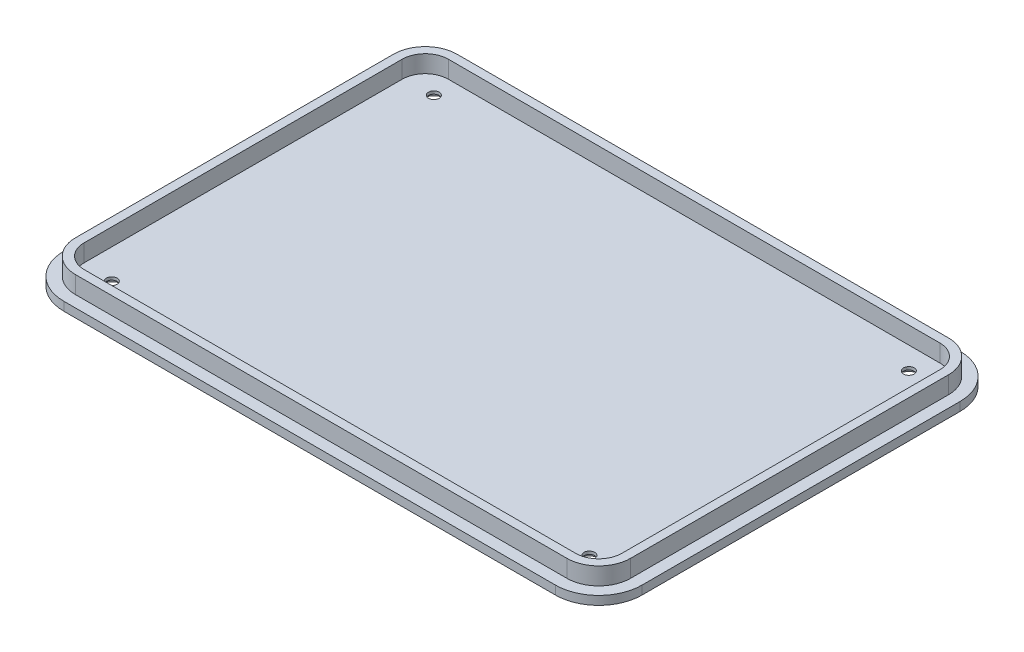
SolidWorks part; units mm, degrees
ref_plane "Front Plane" through (0, 0, 0) normal (0, 0, 1) x (1, 0, 0)
ref_plane "Top Plane" through (0, 0, 0) normal (0, 1, 0) x (1, 0, 0)
ref_plane "Right Plane" through (0, 0, 0) normal (1, 0, 0) x (0, 0, -1)
sketch "Sketch1" plane through (0, 0, 0) normal (0, 1, 0) x (1, 0, 0)
  line L1 (-100, 70) -> (100, 70)
  line L2 (-100, 70) -> (-100, -70)
  line L3 (-100, -70) -> (100, -70)
  line L4 (100, 70) -> (100, -70)
  line L5 (-100, 70) -> (100, -70) construction
  line L6 (-100, -70) -> (100, 70) construction
  point P0 (0, 0)
  dimension "D1" = 140
  dimension "D2" = 200
extrude "Boss-Extrude1" add sketch "Sketch1" along normal blind 3
fillet "Fillet1" radius 15 4 edges at (-100, 1.5, -70) (100, 1.5, -70) (100, 1.5, 70) (-100, 1.5, 70)
sketch "Sketch3" plane through (0, 3, 0) normal (0, 1, 0) x (1, 0, 0)
  line L24 (96, -55) -> (96, 55)
  line L25 (-85, -66) -> (85, -66)
  line L26 (-96, 55) -> (-96, -55)
  line L27 (85, 66) -> (-85, 66)
  line L28 (96, -55) -> (96, 55)
  line L29 (-85, -66) -> (85, -66)
  line L30 (-96, 55) -> (-96, -55)
  line L31 (85, 66) -> (-85, 66)
  line L52 (85, 63) -> (-85, 63)
  line L53 (93, -55) -> (93, 55)
  line L54 (-85, -63) -> (85, -63)
  line L55 (-93, 55) -> (-93, -55)
  line L56 (85, 63) -> (-85, 63)
  line L57 (93, -55) -> (93, 55)
  line L58 (-85, -63) -> (85, -63)
  line L59 (-93, 55) -> (-93, -55)
  arc A20 (96, 55) -> (85, 66) centre (85, 55) ccw
  arc A21 (85, -66) -> (96, -55) centre (85, -55) ccw
  arc A22 (-96, -55) -> (-85, -66) centre (-85, -55) ccw
  arc A23 (-85, 66) -> (-96, 55) centre (-85, 55) ccw
  arc A24 (96, 55) -> (85, 66) centre (85, 55) ccw
  arc A25 (85, -66) -> (96, -55) centre (85, -55) ccw
  arc A26 (-96, -55) -> (-85, -66) centre (-85, -55) ccw
  arc A27 (-85, 66) -> (-96, 55) centre (-85, 55) ccw
  arc A44 (-85, 63) -> (-93, 55) centre (-85, 55) ccw
  arc A45 (93, 55) -> (85, 63) centre (85, 55) ccw
  arc A46 (85, -63) -> (93, -55) centre (85, -55) ccw
  arc A47 (-93, -55) -> (-85, -63) centre (-85, -55) ccw
  arc A48 (-85, 63) -> (-93, 55) centre (-85, 55) ccw
  arc A49 (93, 55) -> (85, 63) centre (85, 55) ccw
  arc A50 (85, -63) -> (93, -55) centre (85, -55) ccw
  arc A51 (-93, -55) -> (-85, -63) centre (-85, -55) ccw
  dimension "D1" = 4
  dimension "D2" = 7
extrude "Boss-Extrude2" add sketch "Sketch3" along normal blind 6
sketch "Sketch4" plane through (0, 0, 0) normal (0, -1, 0) x (-1, 0, 0)
  line L0 (85, -70) -> (-85, -70) construction
  line L6 (100, 55) -> (100, -55) construction
  circle A0 centre (82.73, -55.7) radius 4
  point P0 (0, 0)
  dimension "D3" = 8
  dimension "D1" = 14.3
  dimension "D2" = 17.27
extrude "Cut-Extrude1" cut sketch "Sketch4" against normal blind 2
mirror "Mirror1" about plane through (0, 0, 0) normal (0, 0, 1) of "Cut-Extrude1"
sketch "Sketch5" plane through (0, 2, 0) normal (0, -1, 0) x (1, 0, 0)
  circle A0 centre (-82.73, 55.7) radius 1.85
  dimension "D1" = 3.7
extrude "Cut-Extrude2" cut sketch "Sketch5" against normal blind 6
mirror "Mirror2" about plane through (0, 0, 0) normal (0, 0, 1) of "Cut-Extrude2"
sketch "Sketch6" plane through (0, 0, 0) normal (0, -1, 0) x (-1, 0, 0)
  line L0 (-100, -55) -> (-100, 55) construction
  line L2 (85, -70) -> (-85, -70) construction
  circle A0 centre (-82, -55.25) radius 4
  dimension "D1" = 8
  dimension "D2" = 18
  dimension "D3" = 14.75
extrude "Cut-Extrude3" cut sketch "Sketch6" against normal blind 2
mirror "Mirror3" about plane through (0, 0, 0) normal (0, 0, 1) of "Cut-Extrude3"
sketch "Sketch7" plane through (0, 2, 0) normal (0, -1, 0) x (-1, 0, 0)
  circle A0 centre (-82, -55.25) radius 1.85
  dimension "D1" = 3.7
extrude "Cut-Extrude4" cut sketch "Sketch7" against normal blind 2
mirror "Mirror4" about plane through (0, 0, 0) normal (0, 0, 1) of "Cut-Extrude4"
